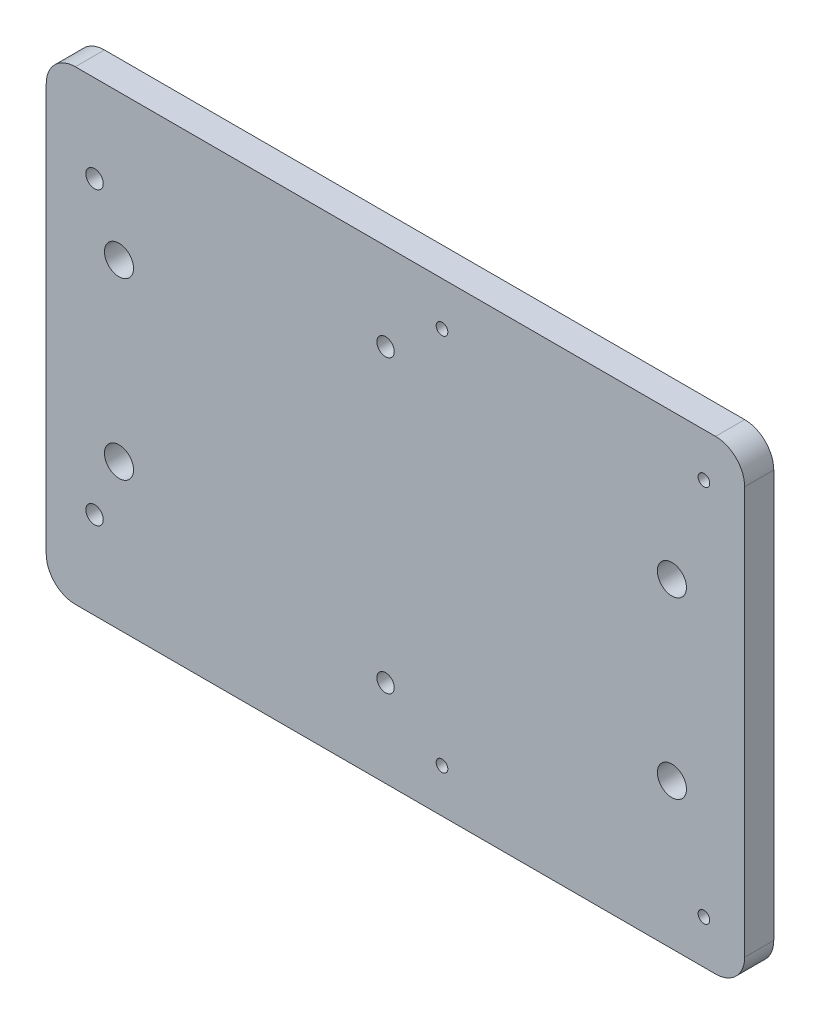
SolidWorks part; units mm, degrees
ref_plane "前视基准面" through (0, 0, 0) normal (0, 0, 1) x (1, 0, 0)
ref_plane "上视基准面" through (0, 0, 0) normal (0, 1, 0) x (1, 0, 0)
ref_plane "右视基准面" through (0, 0, 0) normal (1, 0, 0) x (0, 0, -1)
sketch "草图1" plane through (0, 0, 0) normal (0, 0, 1) x (1, 0, 0)
  line L0 (0, 0) -> (0, 20) construction
  line L1 (-47.5, 15) -> (47.5, 15) construction
  line L2 (-47.5, 15) -> (-47.5, -15) construction
  line L3 (-47.5, -15) -> (47.5, -15) construction
  line L4 (47.5, 15) -> (47.5, -15) construction
  line L5 (-47.5, 15) -> (47.5, -15) construction
  line L6 (-47.5, -15) -> (47.5, 15) construction
  line L7 (0, 0) -> (20, 0) construction
  line L9 (-60, 40) -> (60, 40)
  line L10 (-60, 40) -> (-60, -40)
  line L11 (-60, -40) -> (60, -40)
  line L12 (60, 40) -> (60, -40)
  line L13 (-60, 40) -> (60, -40) construction
  line L14 (-60, -40) -> (60, 40) construction
  circle A0 centre (-47.5, 15) radius 2.5
  circle A1 centre (47.5, 15) radius 2.5
  circle A2 centre (47.5, -15) radius 2.5
  circle A3 centre (-47.5, -15) radius 2.5
  point P0 (0, 0)
  dimension "D3" = 120
  dimension "D1" = 95
  dimension "D2" = 30
  dimension "D4" = 80
extrude "凸台-拉伸1" add sketch "草图1" along normal blind 5
sketch "草图2" plane through (0, 0, 0) normal (0, 0, -1) x (-1, 0, 0)
  line L1 (-60, -40) -> (60, -40)
  line L2 (-60, -40) -> (-60, 40)
  line L3 (-60, 40) -> (60, 40)
  line L4 (60, -40) -> (60, 40)
  line L5 (-60, -40) -> (60, 40) construction
  line L6 (-60, 40) -> (60, -40) construction
  line L7 (-56, 36) -> (56, 36)
  line L8 (-56, 36) -> (-56, -36)
  line L9 (-56, -36) -> (56, -36)
  line L10 (56, 36) -> (56, -36)
  line L11 (-56, 36) -> (56, -36) construction
  line L12 (-56, -36) -> (56, 36) construction
  point P0 (0, 0)
  point P5 (0, 0)
  dimension "D1" = 72
  dimension "D2" = 112
sketch "草图3" plane through (0, 0, 0) normal (0, 0, -1) x (-1, 0, 0)
  circle A0 centre (51.7023, -25) radius 1.5
  circle A1 centre (1.7023, -25) radius 1.5
  circle A2 centre (1.7023, 25) radius 1.5
  circle A3 centre (51.7023, 25) radius 1.5
  circle A4 centre (-8, -32.5) radius 1
  circle A5 centre (-53, -32.5) radius 1
  circle A6 centre (-53, 32.5) radius 1
  circle A7 centre (-8, 32.5) radius 1
extrude "切除-拉伸1" cut sketch "草图3" against normal blind 10
fillet "圆角1" radius 5 4 edges at (-60, -40, 2.5) (-60, 40, 2.5) (60, 40, 2.5) (60, -40, 2.5)
